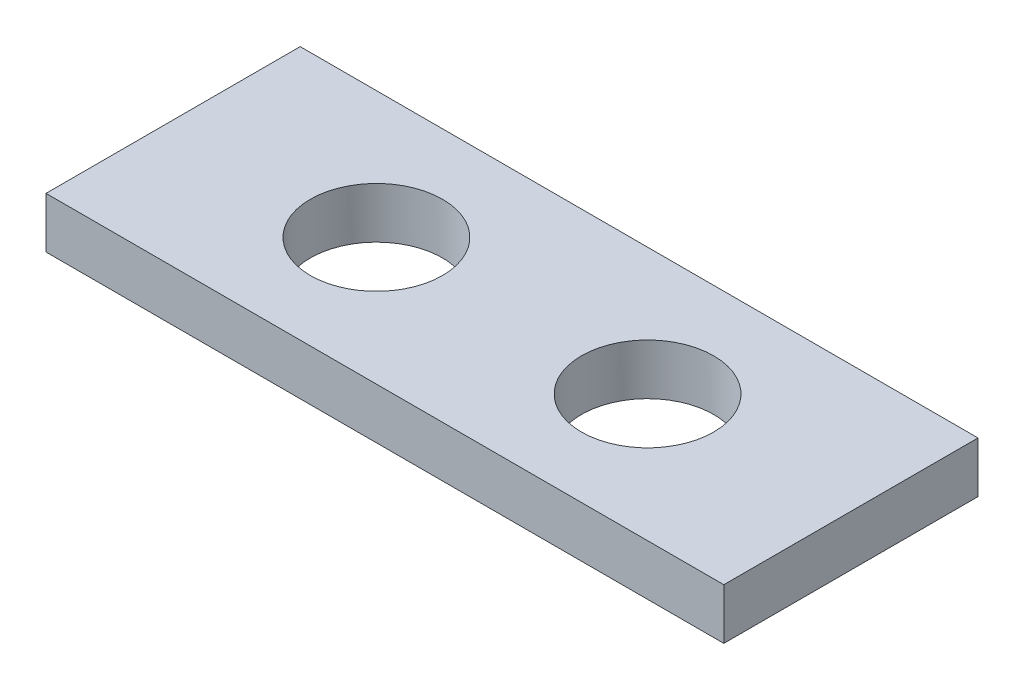
SolidWorks part; units mm, degrees
ref_plane "Front Plane" through (0, 0, 0) normal (0, 0, 1) x (1, 0, 0)
ref_plane "Top Plane" through (0, 0, 0) normal (0, 1, 0) x (1, 0, 0)
ref_plane "Right Plane" through (0, 0, 0) normal (1, 0, 0) x (0, 0, -1)
sketch "Sketch1" plane through (0, 0, 0) normal (0, 1, 0) x (1, 0, 0)
  line L1 (-20, -7.5) -> (20, -7.5)
  line L2 (-20, -7.5) -> (-20, 7.5)
  line L3 (-20, 7.5) -> (20, 7.5)
  line L4 (20, -7.5) -> (20, 7.5)
  line L5 (-20, -7.5) -> (20, 7.5) construction
  line L6 (-20, 7.5) -> (20, -7.5) construction
  point P0 (0, 0)
  dimension "D1" = 40
  dimension "D2" = 15
extrude "Boss-Extrude1" add sketch "Sketch1" along normal blind 3
sketch "Sketch2" plane through (0, 3, 0) normal (0, 1, 0) x (1, 0, 0)
  circle A0 centre (-8, 0) radius 3.9
  dimension "D2" = 7.8
  dimension "D1" = 8
extrude "Cut-Extrude1" cut sketch "Sketch2" against normal through all both and the other way through all
mirror "Mirror1" about plane through (0, 0, 0) normal (1, 0, 0) of "Cut-Extrude1"
